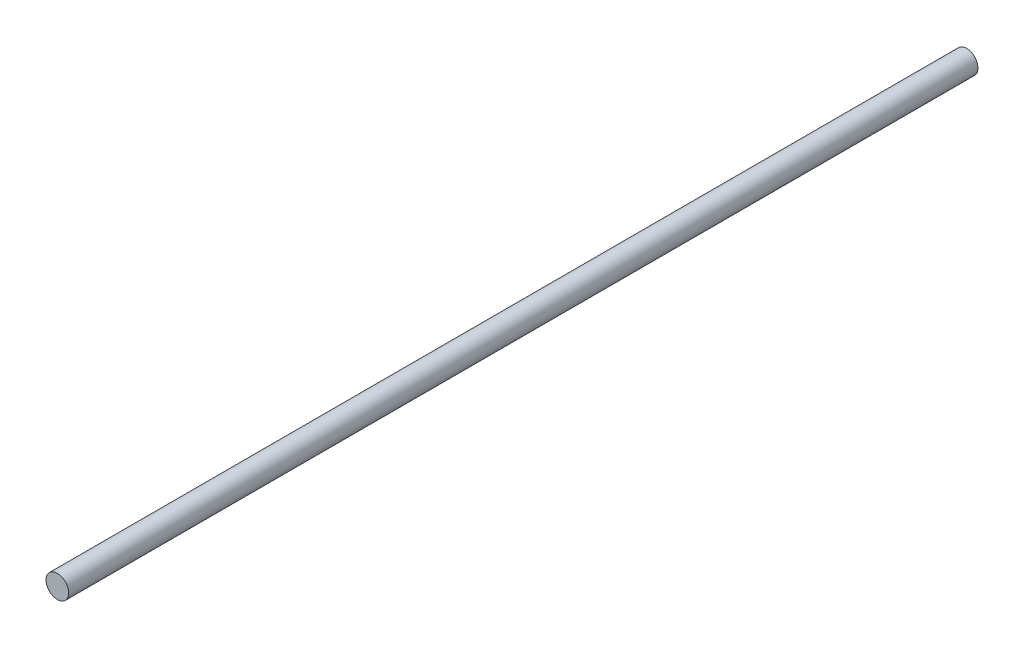
SolidWorks part; units mm, degrees
ref_plane "Plan de face" through (0, 0, 0) normal (0, 0, 1) x (1, 0, 0)
ref_plane "Plan de dessus" through (0, 0, 0) normal (0, 1, 0) x (1, 0, 0)
ref_plane "Plan de droite" through (0, 0, 0) normal (1, 0, 0) x (0, 0, -1)
sketch "Esquisse1" plane through (0, 0, 0) normal (0, 0, 1) x (1, 0, 0)
  circle A0 centre (0, 0) radius 1
  dimension "D1" = 2
extrude "Boss.-Extru.1" add sketch "Esquisse1" along normal blind 80
